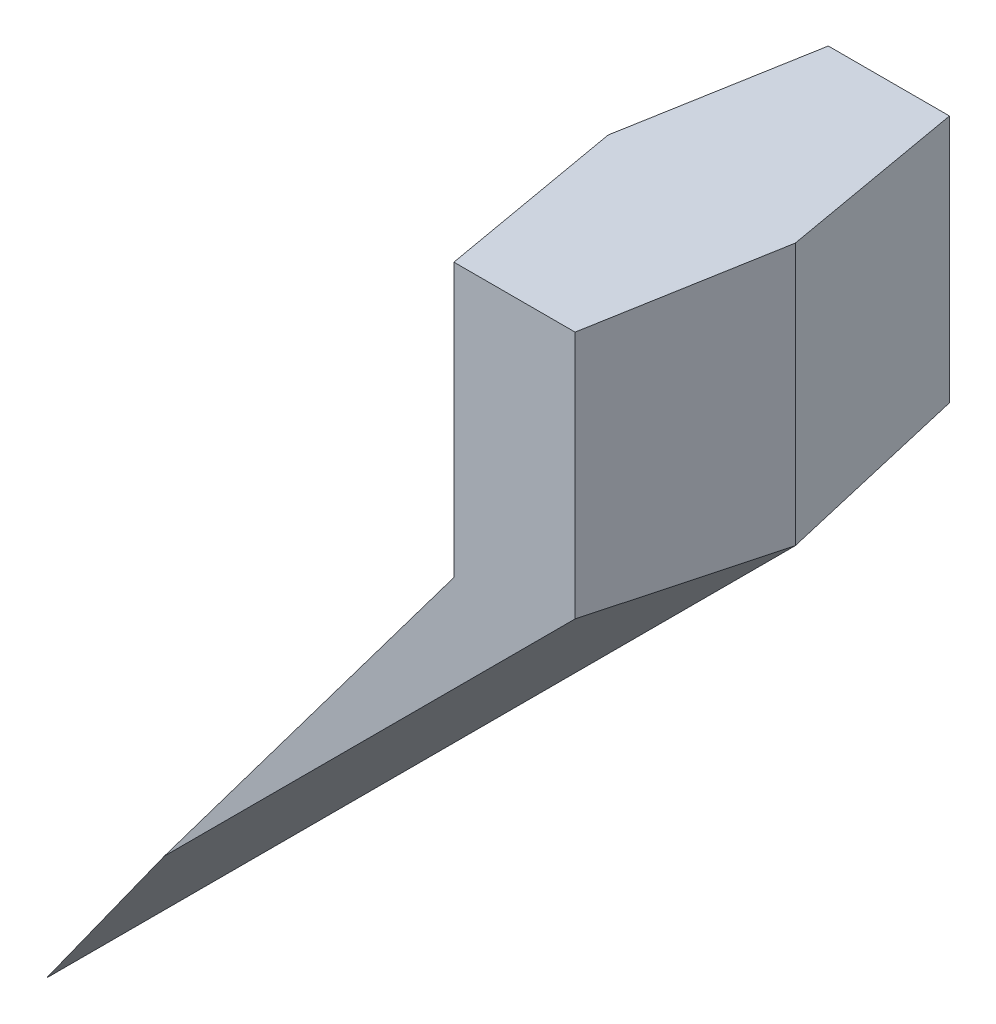
SolidWorks part; units mm, degrees
ref_plane "前视基准面" through (0, 0, 0) normal (0, 0, 1) x (1, 0, 0)
ref_plane "上视基准面" through (0, 0, 0) normal (0, 1, 0) x (1, 0, 0)
ref_plane "右视基准面" through (0, 0, 0) normal (1, 0, 0) x (0, 0, -1)
other "Configuration Table"
sketch "草图2" plane through (0, 0, 0) normal (0, 0, 1) x (1, 0, 0)
  line L0 (0, 0) -> (0, 20)
  line L1 (0, 20) -> (10, 20)
  line L2 (10, 20) -> (10, 0)
  line L3 (10, 0) -> (-30, -40)
  line L4 (-30, -40) -> (0, 0)
  dimension "D1" = 60
  dimension "D2" = 20
  dimension "D3" = 20
  dimension "D4" = 135
  dimension "D5" = 10
extrude "凸台-拉伸1" add sketch "草图2" along normal blind 10 draft 10
mirror "镜向1" about plane through (0, 0, 0) normal (0, 0, -1) of "凸台-拉伸1"
sketch "草图3" plane through (0, 0, 0) normal (1, 0, 0) x (0, 0, -1)
  line L0 (0, -1000) -> (0, 49000) construction
sketch "草图4" plane through (0, 0, 0) normal (0, 0, 1) x (1, 0, 0)
  line L1 (26.4281, 56.1905) -> (-18.0768, 56.1905)
  line L2 (26.4281, 56.1905) -> (26.4281, 14)
  line L3 (26.4281, 14) -> (-18.0768, 14)
  line L4 (-18.0768, 56.1905) -> (-18.0768, 14)
  dimension "D1" = 6
extrude "切除-拉伸4" cut sketch "草图4" against normal mid plane 100
